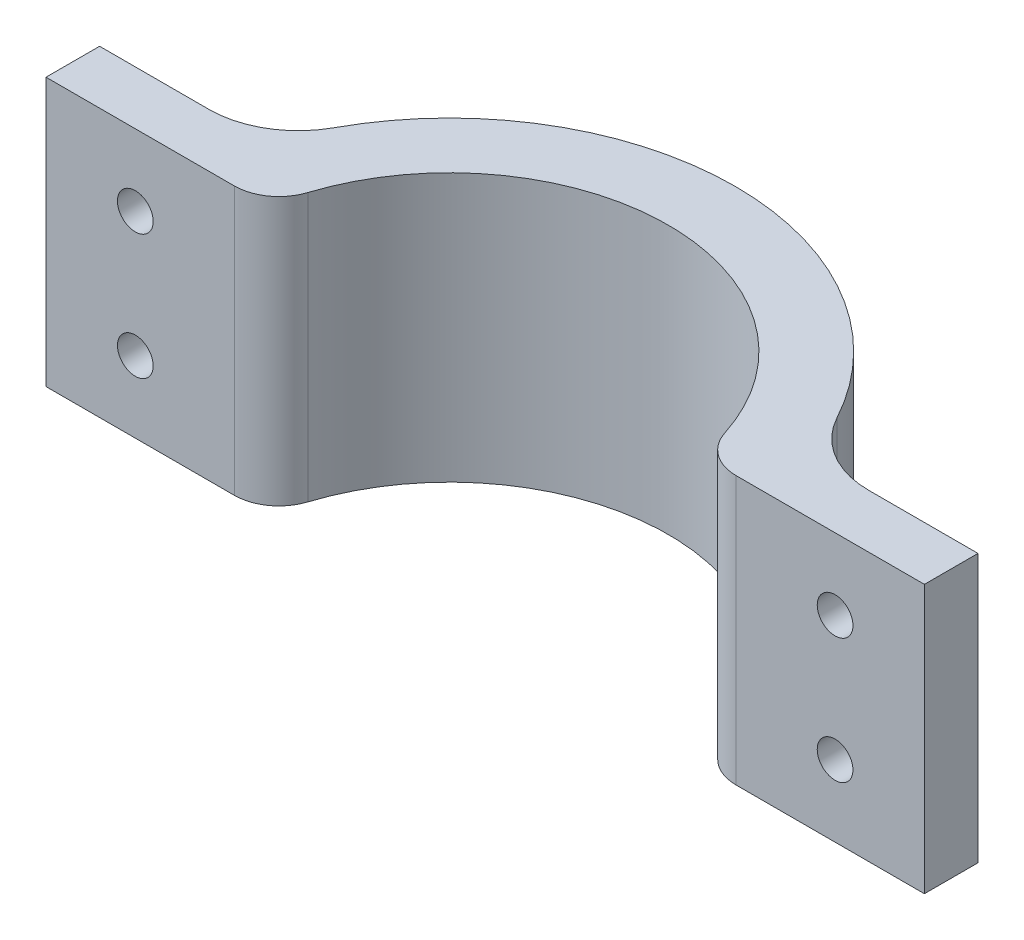
SolidWorks part; units mm, degrees
material "ABS"
ref_plane "Front Plane" through (0, 0, 0) normal (0, 0, 1) x (1, 0, 0)
ref_plane "Top Plane" through (0, 0, 0) normal (0, 1, 0) x (1, 0, 0)
ref_plane "Right Plane" through (0, 0, 0) normal (1, 0, 0) x (0, 0, -1)
sketch "Sketch1" plane through (0, 0, 0) normal (0, 1, 0) x (1, 0, 0)
  line L0 (-22.3663, 10) -> (-30.3974, 10)
  line L1 (-24.1713, 10) -> (-24.1713, 4)
  line L2 (-24.1713, 4) -> (-24.1713, 10)
  line L3 (-24.1713, 4) -> (-49.1713, 4)
  line L4 (-24.1713, 10) -> (-49.1713, 10)
  line L5 (-49.1713, 4) -> (-49.1713, 10)
  line L6 (0, 0) -> (0, 32) construction
  line L7 (24.1713, 10) -> (49.1713, 10)
  line L8 (49.1713, 4) -> (49.1713, 10)
  line L9 (24.1713, 4) -> (49.1713, 4)
  line L10 (24.1713, 10) -> (24.1713, 4)
  line L11 (22.3663, 10) -> (30.3974, 10)
  circle A0 centre (0, 0) radius 24.5
  circle A1 centre (0, 0) radius 32
  dimension "D1" = 49
  dimension "D2" = 64
  dimension "D3" = 10
  dimension "D4" = 6
  dimension "D5" = 25
extrude "Boss-Extrude1" add sketch "Sketch1" along normal blind 30 contours A1 L4 L5 L3 | A0 L0 L1 | L0 A1 L3 L1 | A0 L6 A1 L0 | L6 A0 L11 L7 A1 | A0 L10 L11 | L9 A1 L7 L10 | A1 L9 L8 L7
sketch "Sketch2" plane through (0, 0, -10) normal (0, 0, -1) x (-1, 0, 0)
  line L0 (-30.3974, 30) -> (-49.1713, 30) construction
  line L1 (-30.3974, 0) -> (-49.1713, 0) construction
  line L2 (-49.1713, 30) -> (-49.1713, 0) construction
  line L3 (0, 0) -> (0, 30) construction
  line L4 (30.3974, 30) -> (-30.3974, 30) construction
  circle A0 centre (-39.1713, 22) radius 2
  circle A1 centre (-39.1713, 8) radius 2
  circle A2 centre (39.1713, 8) radius 2
  circle A3 centre (39.1713, 22) radius 2
  dimension "D1" = 4
  dimension "D2" = 4
  dimension "D3" = 8
  dimension "D4" = 8
  dimension "D5" = 10
  dimension "D6" = 10
extrude "Cut-Extrude1" cut sketch "Sketch2" against normal through all
fillet "Fillet1" radius 10 2 edges at (30.3974, 15, -10) (-30.3974, 15, -10)
fillet "Fillet2" radius 5 2 edges at (-24.1713, 15, -4) (24.1713, 15, -4)
